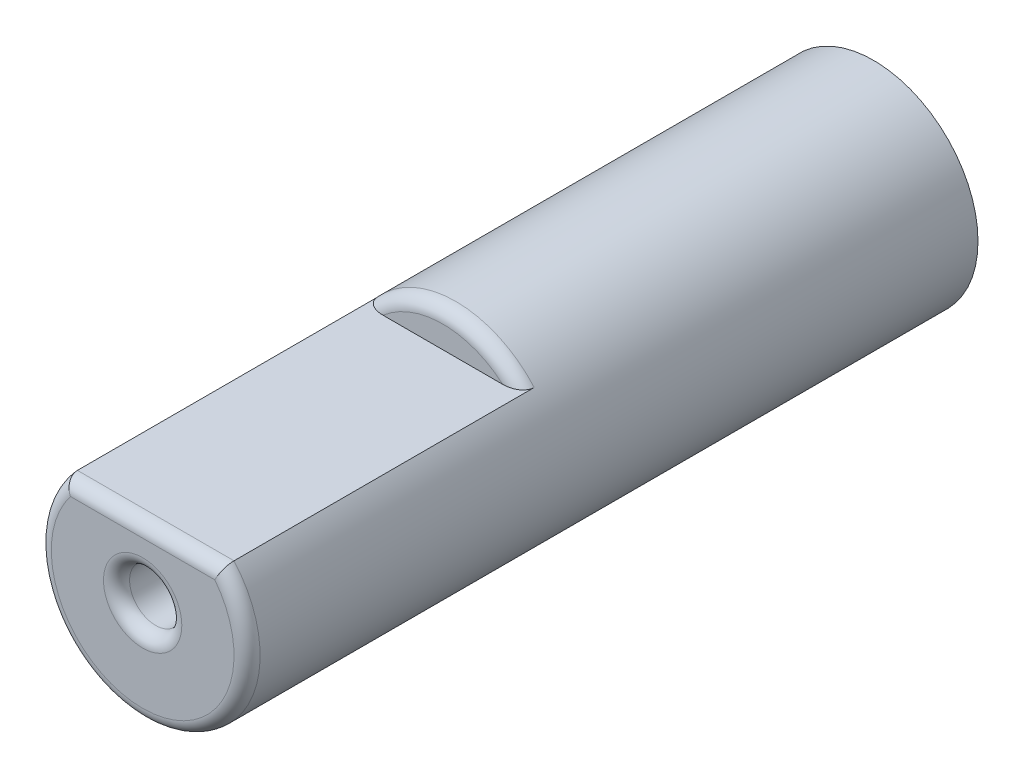
SolidWorks part; units mm, degrees
ref_plane "Front Plane" through (0, 0, 0) normal (0, 0, 1) x (1, 0, 0)
ref_plane "Top Plane" through (0, 0, 0) normal (0, 1, 0) x (1, 0, 0)
ref_plane "Right Plane" through (0, 0, 0) normal (1, 0, 0) x (0, 0, -1)
sketch "Sketch1" plane through (0, 0, 0) normal (0, 0, 1) x (1, 0, 0)
  circle A0 centre (0, 0) radius 4
  dimension "D1" = 8
extrude "Boss-Extrude1" add sketch "Sketch1" along normal blind 28
sketch "Sketch2" plane through (0, 0, 28) normal (0, 0, 1) x (1, 0, 0)
  line L0 (0, 0) -> (0, 2.6458) construction
  line L1 (-3, 2.6458) -> (3, 2.6458)
  circle A0 centre (0, 0) radius 4 construction
  arc A1 (-3, 2.6458) -> (3, 2.6458) centre (0, 0) cw
  circle M1 centre (0, 0) radius 4
  dimension "D1" = 6
extrude "Cut-Extrude1" cut sketch "Sketch2" against normal blind 11.5 contours L1 M1
sketch "Sketch3" plane through (0, 0, 28) normal (0, 0, 1) x (1, 0, 0)
  circle A0 centre (0, 0) radius 1
  dimension "D1" = 2
extrude "Cut-Extrude2" cut sketch "Sketch3" against normal blind 4
fillet "Fillet1" radius 0.5 4 edges at (0, 4, 16.5) (0, 2.6458, 28) (0, -4, 28) (1, 0, 28)
